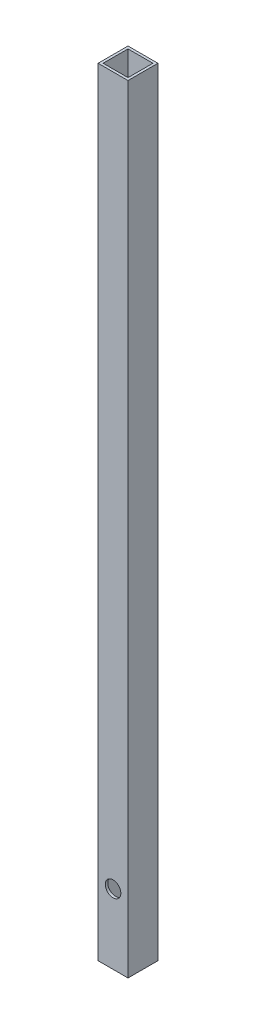
SolidWorks part; units mm, degrees
material "1060 Alloy"
ref_plane "Front Plane" through (0, 0, 0) normal (0, 0, 1) x (1, 0, 0)
ref_plane "Top Plane" through (0, 0, 0) normal (0, 1, 0) x (1, 0, 0)
ref_plane "Right Plane" through (0, 0, 0) normal (1, 0, 0) x (0, 0, -1)
sketch "Sketch1" plane through (0, 0, 0) normal (0, 1, 0) x (1, 0, 0)
  line L0 (-7.9375, 7.9375) -> (-7.9375, -7.9375)
  line L1 (-9.525, 9.525) -> (9.525, 9.525)
  line L2 (-9.525, 9.525) -> (-9.525, -9.525)
  line L3 (-9.525, -9.525) -> (9.525, -9.525)
  line L4 (9.525, 9.525) -> (9.525, -9.525)
  line L5 (-9.525, 9.525) -> (9.525, -9.525) construction
  line L6 (-9.525, -9.525) -> (9.525, 9.525) construction
  line L7 (-7.9375, -7.9375) -> (7.9375, -7.9375)
  line L8 (7.9375, 7.9375) -> (7.9375, -7.9375)
  line L9 (-7.9375, 7.9375) -> (7.9375, 7.9375)
  point P0 (0, 0)
  dimension "D1" = 19.05
  dimension "D2" = 19.05
  dimension "D3" = 1.5875
extrude "Boss-Extrude1" add sketch "Sketch1" along normal blind 495.3
sketch "Sketch2" plane through (0, 0, 9.525) normal (0, 0, 1) x (1, 0, 0)
  line L0 (-9.525, 0) -> (9.525, 0) construction
  line L1 (-9.525, 495.3) -> (-9.525, 0) construction
  circle A1 centre (0, 44.45) radius 4.9609
  dimension "D3" = 9.9219
  dimension "D1" = 44.45
  dimension "D2" = 9.525
extrude "Cut-Extrude1" cut sketch "Sketch2" against normal up to surface (1.5875 mm away) up to face at (0, 247.65, 7.9375)
sketch "Sketch3" plane through (-9.525, 0, 0) normal (-1, 0, 0) x (0, 0, 1)
  line L0 (-9.525, 0) -> (9.525, 0) construction
  circle A0 centre (0, 9.525) radius 0.889
  dimension "D1" = 1.778
  dimension "D2" = 9.525
extrude "Cut-Extrude2" cut sketch "Sketch3" against normal up to next
